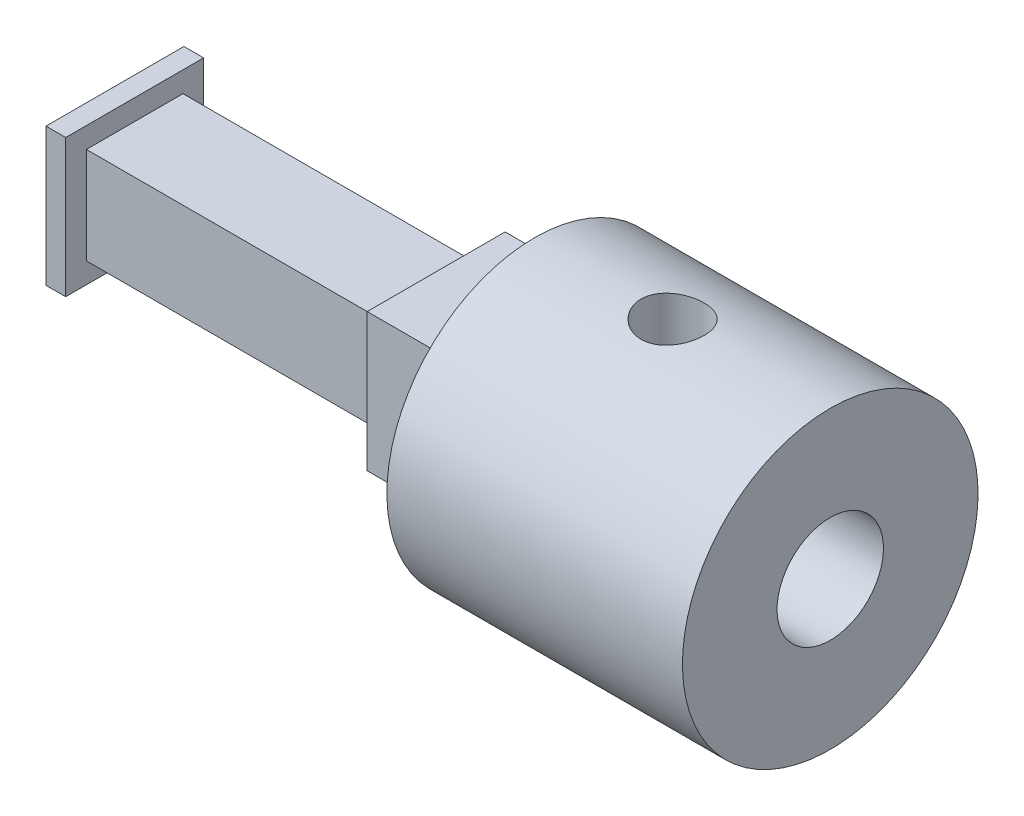
SolidWorks part; units mm, degrees
ref_plane "Front Plane" through (0, 0, 0) normal (0, 0, 1) x (1, 0, 0)
ref_plane "Top Plane" through (0, 0, 0) normal (0, 1, 0) x (1, 0, 0)
ref_plane "Right Plane" through (0, 0, 0) normal (1, 0, 0) x (0, 0, -1)
sketch "Sketch2" plane through (0, 0, 0) normal (0, 0, 1) x (1, 0, 0)
  line L0 (15, 0) -> (15, 7.5)
  line L1 (8.25, 0) -> (-8.25, 0) construction
  line L2 (15, 7.5) -> (0, 7.5)
  line L3 (0, 7.5) -> (0, 0)
  line L6 (0, -8.25) -> (0, 8.25) construction
  line L7 (15, 0) -> (-25, 0) construction
  line L8 (15, 0) -> (-25, 0)
  point P10 (0, 3.75)
  dimension "D1" = 7.5
  dimension "D3" = 15
revolve "Revolve1" add sketch "Sketch2" angle 360 about L8
sketch "Sketch3" plane through (15, 0, 0) normal (1, 0, 0) x (0, 0, -1)
  line L0 (-1.5, 2) -> (1.5, 2) construction
  line L1 (8.25, 0) -> (-8.25, 0) construction
  line L2 (-1.5652, 2.2) -> (1.5652, 2.2) construction
  arc A0 (-1.5, 2) -> (1.5, 2) centre (0, 0) ccw construction
  circle A1 centre (0, 0) radius 2.7
  arc A2 (-1.5652, 2.2) -> (1.5652, 2.2) centre (0, 0) ccw construction
  dimension "D1" = 5
  dimension "D4" = 5.4
  dimension "D2" = 2
  dimension "D3" = 0.2
extrude "Cut-Extrude1" cut sketch "Sketch3" against normal blind 10 contours L2 A1 | L2 A1
sketch "Sketch5" plane through (0, 0, 0) normal (0, 1, 0) x (1, 0, 0)
  line L0 (-8.25, 0) -> (8.25, 0) construction
  line L1 (15, -7.5) -> (15, 7.5) construction
  circle A0 centre (7, 0) radius 1.6
  dimension "D1" = 8
  dimension "D2" = 3.2
extrude "Cut-Extrude2" cut sketch "Sketch5" along normal blind 11
sketch "Sketch6" plane through (0, 0, 0) normal (-1, 0, 0) x (0, 0, 1)
  line L1 (3.5, -3.5) -> (-3.5, -3.5)
  line L2 (3.5, -3.5) -> (3.5, 3.5)
  line L3 (3.5, 3.5) -> (-3.5, 3.5)
  line L4 (-3.5, -3.5) -> (-3.5, 3.5)
  line L5 (3.5, -3.5) -> (-3.5, 3.5) construction
  line L6 (3.5, 3.5) -> (-3.5, -3.5) construction
  point P0 (0, 0)
  dimension "D1" = 7
  dimension "D2" = 7
extrude "Boss-Extrude1" add sketch "Sketch6" along normal blind 5
sketch "Sketch7" plane through (-5, 0, 0) normal (-1, 0, 0) x (0, 0, 1)
  line L1 (-2.45, -2.45) -> (2.45, -2.45)
  line L2 (-2.45, -2.45) -> (-2.45, 2.45)
  line L3 (-2.45, 2.45) -> (2.45, 2.45)
  line L4 (2.45, -2.45) -> (2.45, 2.45)
  line L5 (-2.45, -2.45) -> (2.45, 2.45) construction
  line L6 (-2.45, 2.45) -> (2.45, -2.45) construction
  point P0 (0, 0)
  dimension "D1" = 4.9
extrude "Boss-Extrude2" add sketch "Sketch7" along normal blind 15.3
sketch "Sketch8" plane through (-20.3, 0, 0) normal (-1, 0, 0) x (0, 0, 1)
  line L1 (3.5, -3.5) -> (-3.5, -3.5)
  line L2 (3.5, -3.5) -> (3.5, 3.5)
  line L3 (3.5, 3.5) -> (-3.5, 3.5)
  line L4 (-3.5, -3.5) -> (-3.5, 3.5)
  line L5 (3.5, -3.5) -> (-3.5, 3.5) construction
  line L6 (3.5, 3.5) -> (-3.5, -3.5) construction
  point P0 (0, 0)
extrude "Boss-Extrude3" add sketch "Sketch8" along normal blind 1
